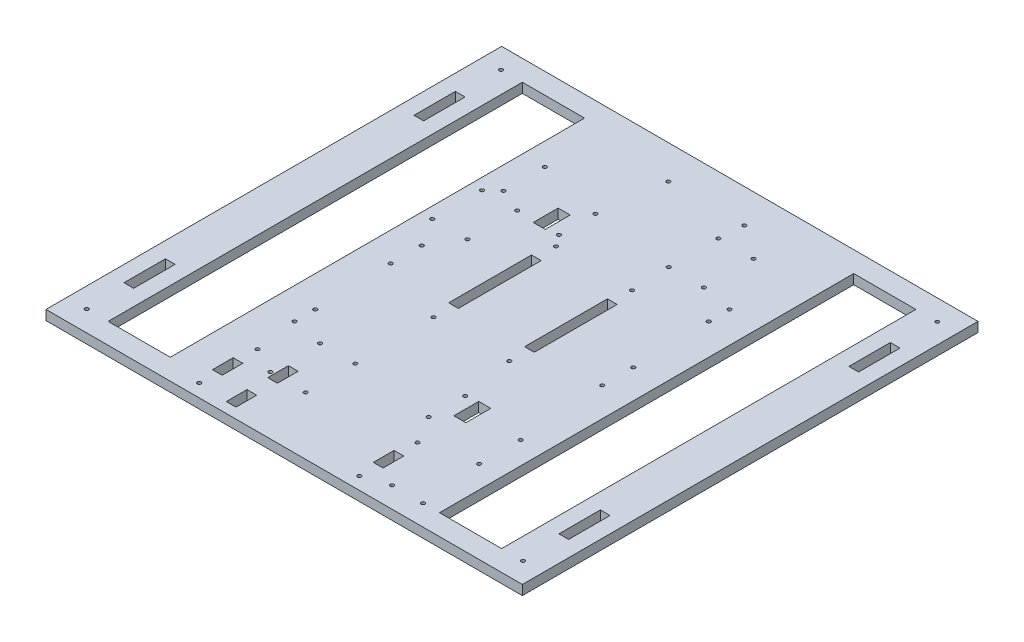
SolidWorks part; units mm, degrees
ref_plane "Front Plane" through (0, 0, 0) normal (0, 0, 1) x (1, 0, 0)
ref_plane "Top Plane" through (0, 0, 0) normal (0, 1, 0) x (1, 0, 0)
ref_plane "Right Plane" through (0, 0, 0) normal (1, 0, 0) x (0, 0, -1)
sketch "Sketch1" plane through (0, 0, 0) normal (0, 1, 0) x (1, 0, 0)
  line L1 (-146.05, 139.7) -> (146.05, 139.7)
  line L2 (-146.05, 139.7) -> (-146.05, -139.7)
  line L3 (-146.05, -139.7) -> (146.05, -139.7)
  line L4 (146.05, 139.7) -> (146.05, -139.7)
  line L5 (-146.05, 139.7) -> (146.05, -139.7) construction
  line L6 (-146.05, -139.7) -> (146.05, 139.7) construction
  point P0 (0, 0)
  dimension "D1" = 279.4
  dimension "D2" = 292.1
extrude "Boss-Extrude1" add sketch "Sketch1" along normal blind 5.9436
sketch "Sketch2" plane through (0, 5.9436, 0) normal (0, 1, 0) x (1, 0, 0)
  line L0 (-146.05, 0) -> (146.05, 0) construction
  line L1 (-120.65, 127) -> (-82.55, 127)
  line L2 (-120.65, 127) -> (-120.65, -127)
  line L3 (-120.65, -127) -> (-82.55, -127)
  line L4 (-82.55, 127) -> (-82.55, -127)
  line L5 (-146.05, 139.7) -> (-146.05, -139.7) construction
  line L6 (146.05, -139.7) -> (146.05, 139.7) construction
  line L7 (0, 139.7) -> (0, -139.7) construction
  line L8 (146.05, 139.7) -> (-146.05, 139.7) construction
  line L9 (-146.05, -139.7) -> (146.05, -139.7) construction
  line L10 (120.65, -127) -> (82.55, -127)
  line L11 (82.55, 127) -> (82.55, -127)
  line L12 (120.65, 127) -> (82.55, 127)
  line L13 (120.65, 127) -> (120.65, -127)
  line L14 (136.3154, 76.2) -> (130.3845, 76.2)
  line L15 (-136.3154, 101.6) -> (-130.3845, 101.6)
  line L16 (-136.3154, 101.6) -> (-136.3154, 76.2)
  line L17 (-136.3154, 76.2) -> (-130.3845, 76.2)
  line L18 (-130.3845, 101.6) -> (-130.3845, 76.2)
  line L19 (130.3845, 101.6) -> (130.3845, 76.2)
  line L20 (136.3154, 101.6) -> (130.3845, 101.6)
  line L21 (136.3154, 101.6) -> (136.3154, 76.2)
  line L22 (136.3154, -101.6) -> (136.3154, -76.2)
  line L23 (136.3154, -101.6) -> (130.3846, -101.6)
  line L24 (130.3846, -101.6) -> (130.3846, -76.2)
  line L25 (136.3154, -76.2) -> (130.3846, -76.2)
  line L26 (-136.3154, -76.2) -> (-130.3845, -76.2)
  line L27 (-130.3845, -101.6) -> (-130.3845, -76.2)
  line L28 (-136.3154, -101.6) -> (-130.3845, -101.6)
  line L29 (-136.3154, -101.6) -> (-136.3154, -76.2)
  line L30 (-133.35, 101.6) -> (-133.35, 76.2) construction
  point P10 (-82.55, 0)
  point P25 (-133.35, 101.6)
  dimension "D1" = 38.1
  dimension "D2" = 254
  dimension "D3" = 25.4
  dimension "D4" = 5.9309
  dimension "D5" = 25.4
  dimension "D6" = 12.7
  dimension "D7" = 25.4
extrude "Cut-Extrude1" cut sketch "Sketch2" against normal through all
sketch "Sketch5" plane through (0, 0, 0) normal (0, -1, 0) x (1, 0, 0)
  line L0 (0, 139.7) -> (0, -139.7) construction
  line L1 (-146.05, 139.7) -> (146.05, 139.7) construction
  line L2 (146.05, -139.7) -> (-146.05, -139.7) construction
  line L3 (-146.05, 0) -> (146.05, 0) construction
  line L4 (-146.05, -139.7) -> (-146.05, 139.7) construction
  line L5 (146.05, 139.7) -> (146.05, -139.7) construction
  line L7 (35.4902, 55.88) -> (42.8562, 55.88)
  line L8 (35.4902, 55.88) -> (35.4902, 71.12)
  line L9 (35.4902, 71.12) -> (42.8562, 71.12)
  line L10 (42.8562, 55.88) -> (42.8562, 71.12)
  line L11 (28.3782, 58.2803) -> (28.3782, 55.5586) construction
  line L15 (-35.4774, -55.88) -> (-42.8434, -55.88)
  line L16 (-35.4774, -55.88) -> (-35.4774, -71.12)
  line L17 (-35.4774, -71.12) -> (-42.8434, -71.12)
  line L18 (-42.8434, -55.88) -> (-42.8434, -71.12)
  line L20 (-146.05, -139.7) -> (-146.05, 139.7) construction
  line L21 (146.05, -139.7) -> (-146.05, -139.7) construction
  circle A0 centre (-43.9938, 104.14) radius 1.1303
  circle A1 centre (-22.4038, 104.14) radius 1.1303
  circle A2 centre (-43.9938, 73.66) radius 1.1303
  circle A3 centre (-22.4038, 73.66) radius 1.1303
  circle A4 centre (28.3782, 79.502) radius 1.1303
  circle A5 centre (28.3781, 57.15) radius 1.1303
  circle A6 centre (68.7616, 88.9) radius 1.1303
  circle A7 centre (68.7616, 63.5) radius 1.1303
  circle A8 centre (-63.5, 69.85) radius 1.1303
  circle A17 centre (44.0065, -73.66) radius 1.1303
  circle A18 centre (44.0065, -104.14) radius 1.1303
  circle A19 centre (22.4165, -104.14) radius 1.1303
  circle A20 centre (22.4165, -73.66) radius 1.1303
  circle A21 centre (-28.3655, -79.502) radius 1.1303
  circle A22 centre (-28.3654, -57.15) radius 1.1303
  circle A23 centre (-68.7489, -63.5) radius 1.1303
  circle A24 centre (-68.7489, -88.9) radius 1.1303
  circle A25 centre (-63.5, 57.15) radius 1.1303
  circle A26 centre (63.5, -69.85) radius 1.1303
  circle A27 centre (63.5, -57.15) radius 1.1303
  circle A28 centre (-64.77, 9.6273) radius 1.1303
  circle A29 centre (-64.77, -9.4227) radius 1.1303
  circle A30 centre (64.77, -9.6103) radius 1.1303
  circle A31 centre (64.77, 9.4397) radius 1.1303
  circle A33 centre (-133.7564, -127) radius 1.1303
  circle A36 centre (-133.7564, 127) radius 1.1303
  circle A37 centre (133.7564, -127) radius 1.1303
  circle A38 centre (133.7564, 127) radius 1.1303
  dimension "D1" = 2.2606
  dimension "D2" = 1.27
  dimension "D3" = 7.366
  dimension "D4" = 15.24
  dimension "D5" = 7.112
  dimension "D6" = 15.24
  dimension "D7" = 7.366
  dimension "D8" = 7.112
  dimension "D9" = 1.27
  dimension "D10" = 12.2936
  dimension "D11" = 12.7
extrude "Cut-Extrude2" cut sketch "Sketch5" against normal through all
sketch "Sketch7" plane through (0, 5.9436, 0) normal (0, 1, 0) x (1, 0, 0)
  line L0 (-60.0696, -88.9) -> (-60.0696, -139.7) construction
  line L1 (-63.0311, -107.95) -> (-57.0875, -107.95)
  line L2 (-63.0311, -107.95) -> (-63.0311, -120.65)
  line L3 (-63.0311, -120.65) -> (-57.0875, -120.65)
  line L4 (-57.0875, -107.95) -> (-57.0875, -120.65)
  line L5 (-41.8475, -95.25) -> (-35.9039, -95.25)
  line L6 (-41.8475, -95.25) -> (-41.8475, -107.95)
  line L7 (-41.8475, -107.95) -> (-35.9039, -107.95)
  line L8 (-35.9039, -95.25) -> (-35.9039, -107.95)
  line L13 (-41.8475, -120.65) -> (-35.9039, -120.65)
  line L14 (-41.8475, -120.65) -> (-41.8475, -133.35)
  line L15 (-41.8475, -133.35) -> (-35.9039, -133.35)
  line L16 (-35.9039, -120.65) -> (-35.9039, -133.35)
  line L17 (35.5555, -107.8579) -> (41.4991, -107.8579)
  line L18 (35.5555, -107.8579) -> (35.5555, -120.5579)
  line L19 (35.5555, -120.5579) -> (41.4991, -120.5579)
  line L20 (41.4991, -107.8579) -> (41.4991, -120.5579)
  line L21 (38.5273, -88.9) -> (38.5273, -139.7) construction
  line L22 (-146.05, -139.7) -> (146.05, -139.7) construction
  circle A0 centre (53.4103, -127) radius 1.1303
  circle A1 centre (72.4603, -127) radius 1.1303
  circle A2 centre (-60.0696, -95.9966) radius 1.1303
  circle A3 centre (-60.0696, -131.7426) radius 1.1303
  circle A4 centre (38.5273, -96.4823) radius 1.1303
  circle A5 centre (38.5273, -132.0622) radius 1.1303
  point P29 (38.5273, -107.8579)
  dimension "D1" = 2.2606
  dimension "D3" = 12.7
  dimension "D5" = 2.2606
  dimension "D2" = 19.05
  dimension "D4" = 5.9436
extrude "Cut-Extrude3" cut sketch "Sketch7" against normal through all
sketch "Sketch9" plane through (0, 5.9436, 0) normal (0, 1, 0) x (1, 0, 0)
  line L0 (20.4724, -25.0867) -> (23.4442, -25.0867) construction
  line L1 (23.4442, -25.0867) -> (26.416, -25.0867) construction
  line L2 (26.416, -26.4287) -> (26.416, -25.0867) construction
  line L3 (26.416, -25.0867) -> (26.416, -23.4823) construction
  line L6 (-26.1112, 117.7036) -> (-26.1112, 119.0393) construction
  line L7 (-26.1112, 119.0393) -> (-23.1394, 119.0393) construction
  line L8 (-20.1676, 119.0393) -> (-23.1394, 119.0393) construction
  circle A1 centre (23.4442, 50.1545) radius 1.1303
  circle A2 centre (23.4442, 119.0393) radius 1.1303
  circle A3 centre (23.4442, -25.0867) radius 1.1303
  circle A7 centre (-23.1394, 119.0393) radius 1.1303
  circle A8 centre (-23.1394, 50.1545) radius 1.1303
  circle A9 centre (-23.1394, -25.0867) radius 1.1303
  dimension "D1" = 2.2606
  dimension "D2" = 75.2411
  dimension "D3" = 68.8848
extrude "Cut-Extrude4" cut sketch "Sketch9" against normal through all
sketch "Sketch10" plane through (0, 5.9436, 0) normal (0, 1, 0) x (1, 0, 0)
  line L0 (82.55, 127) -> (82.55, -127) construction
  line L1 (26.416, -12.7349) -> (20.4724, -12.7349)
  line L2 (26.416, -12.7349) -> (26.416, 38.0651)
  line L3 (26.416, 38.0651) -> (20.4724, 38.0651)
  line L4 (20.4724, -12.7349) -> (20.4724, 38.0651)
  line L5 (26.416, -12.7349) -> (20.4724, 38.0651) construction
  line L6 (26.416, 38.0651) -> (20.4724, -12.7349) construction
  line L7 (-20.1676, 38.0651) -> (-26.1112, 38.0651)
  line L8 (-20.1676, 38.0651) -> (-20.1676, -12.7349)
  line L9 (-20.1676, -12.7349) -> (-26.1112, -12.7349)
  line L10 (-26.1112, 38.0651) -> (-26.1112, -12.7349)
  line L11 (-20.1676, 38.0651) -> (-26.1112, -12.7349) construction
  line L12 (-20.1676, -12.7349) -> (-26.1112, 38.0651) construction
  line L13 (146.05, 139.7) -> (-146.05, 139.7) construction
  point P4 (23.4442, 12.6651)
  point P9 (-23.1394, 12.6651)
  dimension "D1" = 5.9436
  dimension "D2" = 50.8
  dimension "D3" = 40.64
  dimension "D4" = 56.134
  dimension "D5" = 101.6349
extrude "Cut-Extrude5" cut sketch "Sketch10" against normal through all
sketch "Sketch12" plane through (0, 5.9436, 0) normal (0, 1, 0) x (1, 0, 0)
  circle A1 centre (-75.6666, 26.7462) radius 1.1303
  circle A2 centre (-75.6666, 57.2262) radius 1.1303
  circle A3 centre (-54.0766, 57.2262) radius 1.1303
  circle A4 centre (-54.0766, 26.7462) radius 1.1303
  dimension "D1" = 2.2606
extrude "Cut-Extrude6" cut sketch "Sketch12" against normal through all
